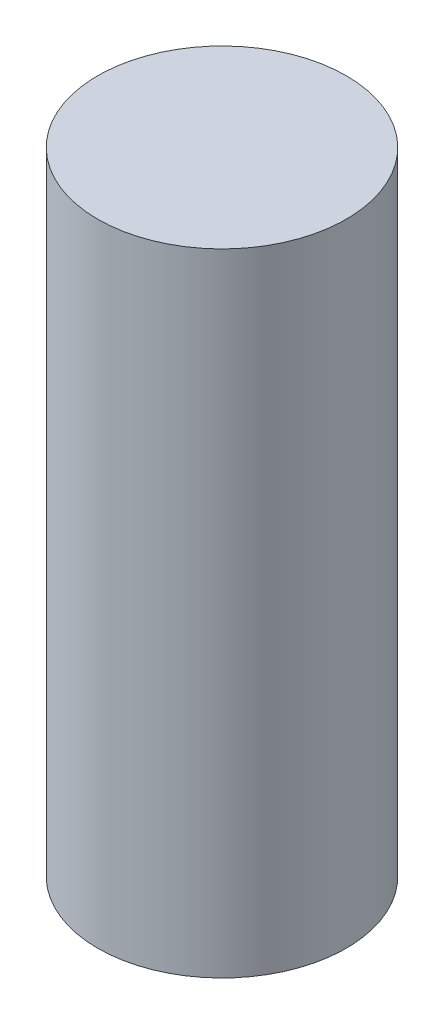
SolidWorks part; units mm, degrees
ref_plane "Front Plane" through (0, 0, 0) normal (0, 0, 1) x (1, 0, 0)
ref_plane "Top Plane" through (0, 0, 0) normal (0, 1, 0) x (1, 0, 0)
ref_plane "Right Plane" through (0, 0, 0) normal (1, 0, 0) x (0, 0, -1)
sketch "Sketch1" plane through (0, 0, 0) normal (0, 1, 0) x (1, 0, 0)
  circle A0 centre (0, 0) radius 1.5
  dimension "D1" = 3
extrude "Extrude1" add sketch "Sketch1" along normal blind 7.62
